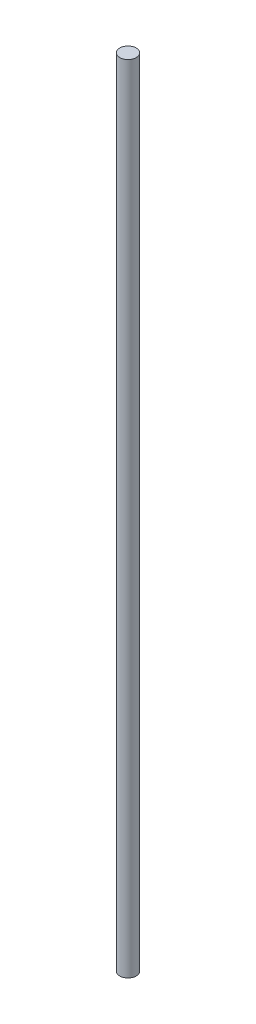
SolidWorks part; units mm, degrees
ref_plane "Front Plane" through (0, 0, 0) normal (0, 0, 1) x (1, 0, 0)
ref_plane "Top Plane" through (0, 0, 0) normal (0, 1, 0) x (1, 0, 0)
ref_plane "Right Plane" through (0, 0, 0) normal (1, 0, 0) x (0, 0, -1)
sketch "Sketch1" plane through (0, 0, 0) normal (0, 1, 0) x (1, 0, 0)
  circle A0 centre (0, 0) radius 19.05
extrude "Boss-Extrude1" add sketch "Sketch1" along normal blind 1828.8
